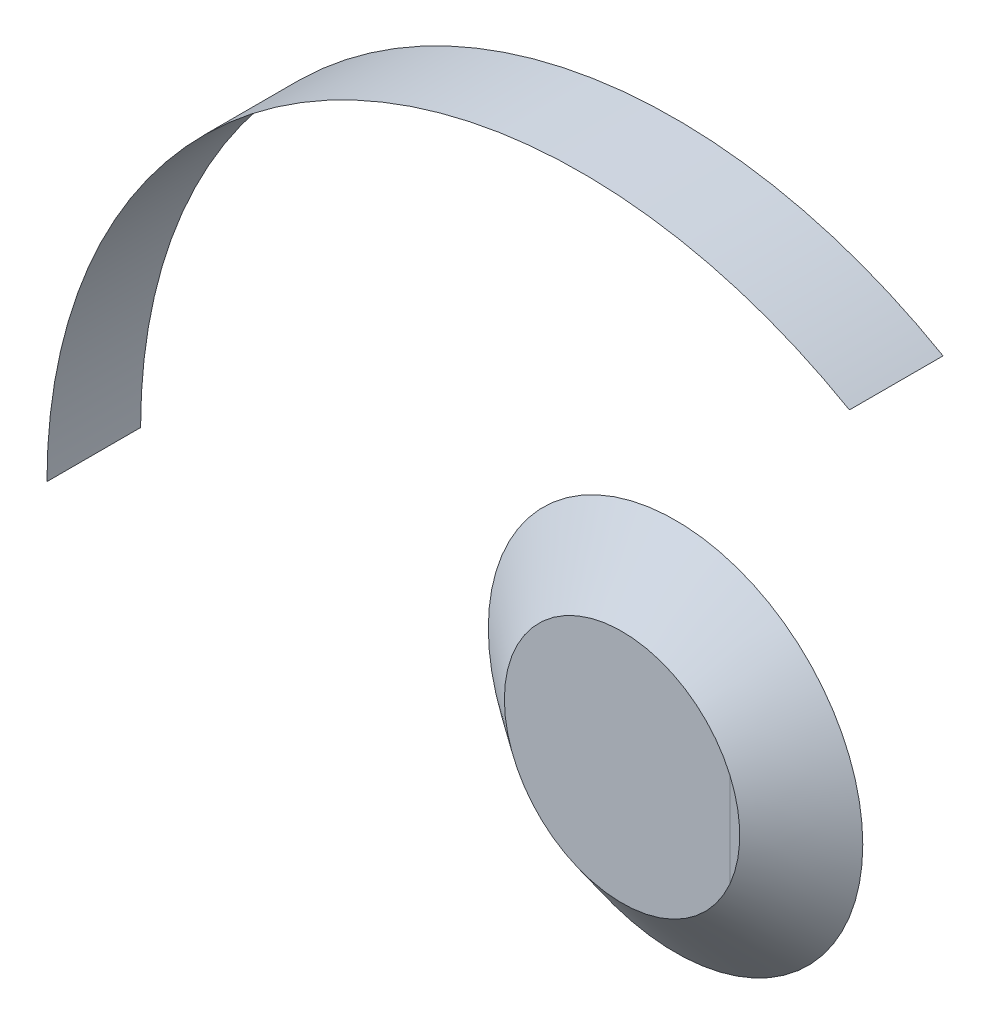
SolidWorks part; units mm, degrees
ref_plane "前视基准面" through (0, 0, 0) normal (0, 0, 1) x (1, 0, 0)
ref_plane "上视基准面" through (0, 0, 0) normal (0, 1, 0) x (1, 0, 0)
ref_plane "右视基准面" through (0, 0, 0) normal (1, 0, 0) x (0, 0, -1)
sketch "草图1" plane through (0, 0, 0) normal (0, 0, 1) x (1, 0, 0)
  circle A0 centre (0, 0) radius 44
  dimension "D1" = 88
extrude "凸台-拉伸1" add sketch "草图1" along normal blind 20
sketch "草图4" plane through (0, 0, 0) normal (0, 0, -1) x (-1, 0, 0)
  circle A0 centre (0, 0) radius 70
  dimension "D1" = 140
loft "放样3" add profiles "草图4" section edge at (44, 0, 20) section "草图4"
sketch "草图5" plane through (0, 0, 0) normal (0, 0, -1) x (-1, 0, 0)
  line L0 (0, 0) -> (200, 0) construction
  line L1 (0, 0) -> (-100, 173.2051) construction
  line L2 (-50, 86.6025) -> (100, 173.2051) construction
  arc A0 (200, 0) -> (-100, 173.2051) centre (0, 0) ccw
  dimension "D1" = 400
  dimension "D2" = 120
ref_plane "基准面1" through (0, 0, 0) normal (0, 0, -1) x (-1, 0, 0)
surface "曲面-拉伸1" sketch "草图5" parameters "D1"=35
sketch "草图7" plane through (0, 0, 0) normal (0, 1, 0) x (1, 0, 0)
  line L0 (-200, -35) -> (-200, 0) construction
  line L1 (100, 0) -> (100, -35) construction
  arc A0 (-200, -29.2549) -> (100, -7.0038) centre (-112.6281, 826.2526) ccw
  point P3 (0, 0)
  point P8 (-200, -30.629)
  point P9 (0, 0)
  point P10 (0, 0)
  point P11 (0, 0)
  point P12 (0, 0)
  point P13 (-200, -29.2549)
split line "分割线2"
